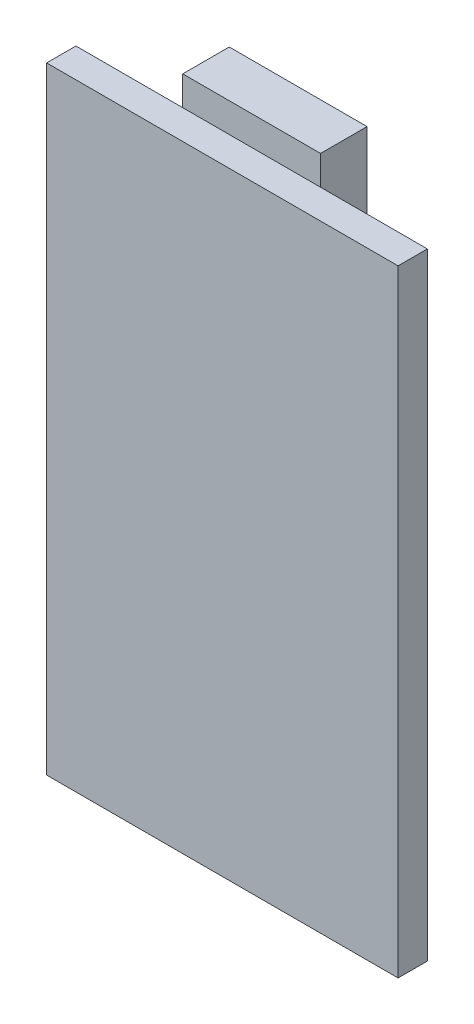
SolidWorks part; units mm, degrees
ref_plane "Front Plane" through (0, 0, 0) normal (0, 0, 1) x (1, 0, 0)
ref_plane "Top Plane" through (0, 0, 0) normal (0, 1, 0) x (1, 0, 0)
ref_plane "Right Plane" through (0, 0, 0) normal (1, 0, 0) x (0, 0, -1)
sketch "Sketch1" plane through (0, 0, 0) normal (0, 0, 1) x (1, 0, 0)
  line L1 (-10.2, 0) -> (10.2, 0)
  line L2 (-10.2, 0) -> (-10.2, -35.8)
  line L3 (-10.2, -35.8) -> (10.2, -35.8)
  line L4 (10.2, 0) -> (10.2, -35.8)
  dimension "D1" = 35.8
  dimension "D2" = 20.4
extrude "Boss-Extrude1" add sketch "Sketch1" against normal blind 1.7
sketch "Sketch2" plane through (0, 0, -1.7) normal (0, 0, -1) x (-1, 0, 0)
  line L1 (-4, 1.7) -> (4, 1.7)
  line L2 (-4, 1.7) -> (-4, -4.1)
  line L3 (-4, -4.1) -> (4, -4.1)
  line L4 (4, 1.7) -> (4, -4.1)
  line L5 (-10.2, 0) -> (10.2, 0) construction
  line L6 (0, 1.7) -> (0, 0) construction
  dimension "D1" = 8
  dimension "D2" = 5.8
  dimension "D3" = 1.7
extrude "Boss-Extrude2" add sketch "Sketch2" along normal blind 2.7
